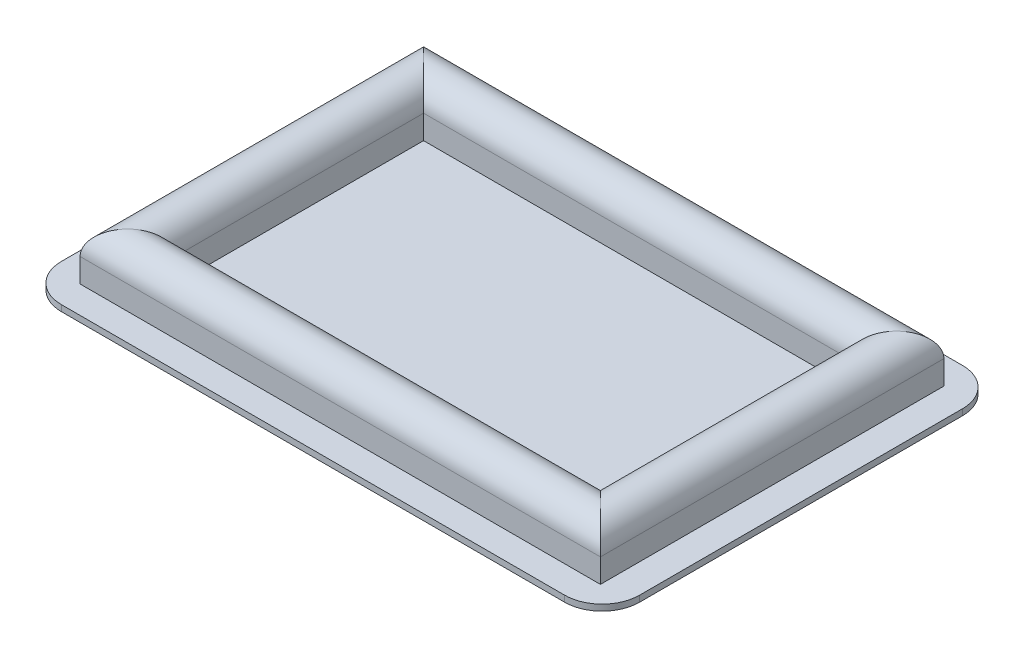
SolidWorks part; units mm, degrees
ref_plane "Front Plane" through (0, 0, 0) normal (0, 0, 1) x (1, 0, 0)
ref_plane "Top Plane" through (0, 0, 0) normal (0, 1, 0) x (1, 0, 0)
ref_plane "Right Plane" through (0, 0, 0) normal (1, 0, 0) x (0, 0, -1)
sketch "Sketch1" plane through (0, 0, 0) normal (0, 1, 0) x (1, 0, 0)
  line L1 (37, -29.25) -> (-37, -29.25)
  line L2 (42.5, -23.75) -> (42.5, 23.75)
  line L3 (37, 29.25) -> (-37, 29.25)
  line L4 (-42.5, -23.75) -> (-42.5, 23.75)
  line L5 (42.5, -29.25) -> (-42.5, 29.25) construction
  line L6 (42.5, 29.25) -> (-42.5, -29.25) construction
  arc A0 (-37, -29.25) -> (-42.5, -23.75) centre (-37, -23.75) cw
  arc A1 (37, -29.25) -> (42.5, -23.75) centre (37, -23.75) ccw
  arc A2 (42.5, 23.75) -> (37, 29.25) centre (37, 23.75) ccw
  arc A3 (-37, 29.25) -> (-42.5, 23.75) centre (-37, 23.75) ccw
  point P0 (0, 0)
  dimension "D3" = 5.5
  dimension "D1" = 85
  dimension "D2" = 58.5
extrude "Boss-Extrude1" add sketch "Sketch1" along normal blind 0.9
sketch "Sketch2" plane through (0, 0.9, 0) normal (0, 1, 0) x (1, 0, 0)
  line L1 (34.75, -21.75) -> (-34.75, -21.75)
  line L2 (34.75, -21.75) -> (34.75, 21.75)
  line L3 (34.75, 21.75) -> (-34.75, 21.75)
  line L4 (-34.75, -21.75) -> (-34.75, 21.75)
  line L5 (34.75, -21.75) -> (-34.75, 21.75) construction
  line L6 (34.75, 21.75) -> (-34.75, -21.75) construction
  point P0 (0, 0)
  dimension "D1" = 43.5
  dimension "D2" = 69.5
sketch "Sketch3" plane through (0, 0, 0) normal (0, 0, 1) x (1, 0, 0)
  line L0 (34.75, 0.9) -> (-34.75, 0.9) construction
  line L2 (-37, 0.9) -> (-42.5, 0.9) construction
  line L3 (-38.25, 0.9) -> (-31.25, 0.9)
  line L4 (-38.25, 0.9) -> (-38.25, 4.4)
  line L5 (-31.25, 0.9) -> (-31.25, 4.4)
  arc A1 (-38.25, 4.4) -> (-31.25, 4.4) centre (-34.75, 4.4) cw
  dimension "D1" = 3.5
  dimension "D2" = 3.5
sweep "Sweep1" add profiles "Sketch3" path "Sketch2"
sketch "Sketch4" plane through (0, 0.9, 0) normal (0, 1, 0) x (1, 0, 0)
  point P0 (0, 0)
